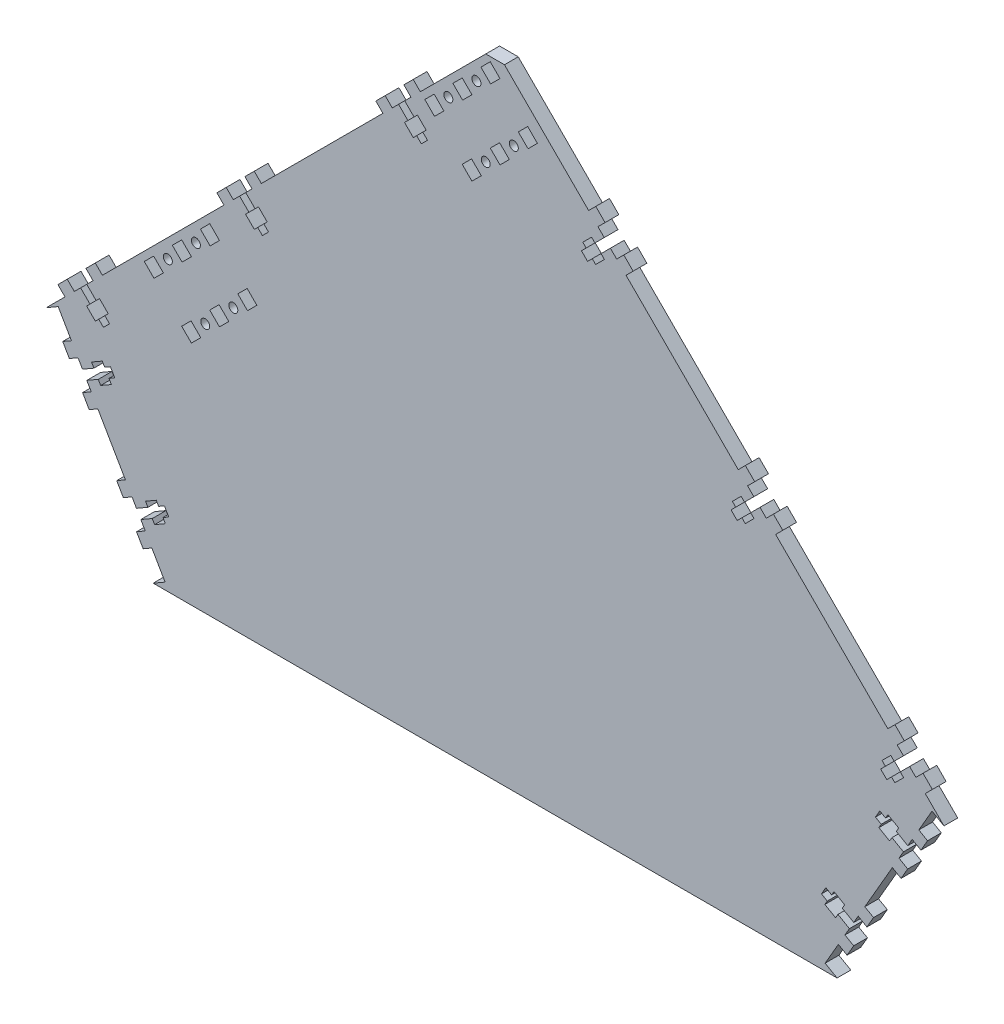
SolidWorks part; units mm, degrees
material "Acrylic (Blue)"
ref_plane "Front Plane" through (0, 0, 0) normal (0, 0, 1) x (1, 0, 0)
ref_plane "Top Plane" through (0, 0, 0) normal (0, 1, 0) x (1, 0, 0)
ref_plane "Right Plane" through (0, 0, 0) normal (1, 0, 0) x (0, 0, -1)
sketch "Sketch1" plane through (0, 0, 0) normal (0, 0, 1) x (1, 0, 0)
  line L0 (0, 0) -> (0, 304.4261) construction
  line L1 (0, 304.4261) -> (215.5261, 88.9)
  line L2 (215.5261, 88.9) -> (164.1997, 0)
  line L3 (164.1997, 0) -> (0, 0)
  line L4 (0, 304.4261) -> (-215.5261, 88.9)
  line L5 (-215.5261, 88.9) -> (-164.1997, 0)
  line L6 (-164.1997, 0) -> (0, 0)
  line L7 (-215.5261, 88.9) -> (215.5261, 88.9) construction
  line L8 (0, 304.4261) -> (3.5921, 308.0182) construction
  line L9 (3.5921, 308.0182) -> (219.1182, 92.4921) construction
  line L10 (219.1182, 92.4921) -> (215.5261, 88.9) construction
  line L11 (3.5921, 308.0182) -> (0, 311.6104) construction
  line L12 (0, 311.6104) -> (-219.1182, 92.4921) construction
  line L13 (-219.1182, 92.4921) -> (-215.5261, 88.9) construction
  line L14 (215.5261, 88.9) -> (219.9256, 86.36) construction
  line L15 (219.9256, 86.36) -> (168.5991, -2.54) construction
  line L16 (168.5991, -2.54) -> (164.1997, 0) construction
  line L17 (164.1997, 0) -> (164.1997, -12.7) construction
  line L18 (164.1997, -12.7) -> (-164.1997, -12.7) construction
  line L19 (-164.1997, -12.7) -> (-164.1997, 0) construction
  line L20 (-164.1997, 0) -> (-168.5991, -2.54) construction
  line L21 (-168.5991, -2.54) -> (-219.9256, 86.36) construction
  line L22 (-219.9256, 86.36) -> (-215.5261, 88.9) construction
  dimension "D1" = 304.8
  dimension "D2" = 120
  dimension "D3" = 88.9
  dimension "D4" = 5.08
  dimension "D5" = 12.7
extrude "Boss-Extrude1" add sketch "Sketch1" along normal blind 6.604
sketch "Sketch8" plane through (0, 0, 6.604) normal (0, 0, 1) x (1, 0, 0)
  line L0 (0, 304.4261) -> (-215.5261, 88.9) construction
  line L1 (215.5261, 88.9) -> (0, 304.4261) construction
  line B0 (-20.2954, 279.8202) -> (-15.8053, 284.3104)
  line B1 (-15.8053, 284.3104) -> (-11.1355, 279.6406)
  line B2 (-11.1355, 279.6406) -> (-15.6256, 275.1505)
  line B3 (-15.6256, 275.1505) -> (-20.2954, 279.8202)
  line B4 (-33.7658, 266.3499) -> (-29.2756, 270.84)
  line B5 (-29.2756, 270.84) -> (-24.6059, 266.1703)
  line B6 (-24.6059, 266.1703) -> (-29.096, 261.6801)
  line B7 (-29.096, 261.6801) -> (-33.7658, 266.3499)
  circle B8 centre (-22.4506, 272.9953) radius 2.1526
  line B9 (-13.4704, 281.9755) -> (-8.9803, 286.4656) construction
  circle B10 centre (-8.9803, 286.4656) radius 2.1527
  line B11 (-2.1553, 288.6209) -> (2.3349, 293.111)
  line B12 (-6.825, 293.2906) -> (-2.3349, 297.7808)
  line B13 (-2.3349, 297.7808) -> (2.3349, 293.111)
  line B14 (-6.825, 293.2906) -> (-2.1553, 288.6209)
  line B15 (-2.3349, 261.8597) -> (2.1553, 266.3499)
  line B16 (2.1553, 266.3499) -> (6.825, 261.6801)
  line B17 (6.825, 261.6801) -> (2.3349, 257.19)
  line B18 (2.3349, 257.19) -> (-2.3349, 261.8597)
  line B19 (-15.8053, 248.3893) -> (-11.3151, 252.8795)
  line B20 (-11.3151, 252.8795) -> (-6.6454, 248.2097)
  line B21 (-6.6454, 248.2097) -> (-11.1355, 243.7196)
  line B22 (-11.1355, 243.7196) -> (-15.8053, 248.3893)
  circle B23 centre (-4.4901, 255.0347) radius 2.1526
  circle B24 centre (8.9803, 268.5051) radius 2.1527
  line B25 (15.8053, 270.6604) -> (20.2954, 275.1505)
  line B26 (11.1355, 275.3301) -> (15.6256, 279.8202)
  line B27 (15.6256, 279.8202) -> (20.2954, 275.1505)
  line B28 (11.1355, 275.3301) -> (15.8053, 270.6604)
  line B29 (-154.9992, 145.1164) -> (-150.5091, 149.6065)
  line B30 (-150.5091, 149.6065) -> (-145.8394, 144.9368)
  line B31 (-145.8394, 144.9368) -> (-150.3295, 140.4467)
  line B32 (-150.3295, 140.4467) -> (-154.9992, 145.1164)
  line B33 (-168.4696, 131.646) -> (-163.9795, 136.1361)
  line B34 (-163.9795, 136.1361) -> (-159.3097, 131.4664)
  line B35 (-159.3097, 131.4664) -> (-163.7999, 126.9763)
  line B36 (-163.7999, 126.9763) -> (-168.4696, 131.646)
  circle B37 centre (-157.1545, 138.2914) radius 2.1526
  circle B38 centre (-143.6841, 151.7618) radius 2.1527
  line B39 (-136.8591, 153.9171) -> (-132.369, 158.4072)
  line B40 (-141.5288, 158.5868) -> (-137.0387, 163.0769)
  line B41 (-137.0387, 163.0769) -> (-132.369, 158.4072)
  line B42 (-141.5288, 158.5868) -> (-136.8591, 153.9171)
  line B43 (-137.0387, 127.1559) -> (-132.5486, 131.646)
  line B44 (-132.5486, 131.646) -> (-127.8788, 126.9763)
  line B45 (-127.8788, 126.9763) -> (-132.369, 122.4862)
  line B46 (-132.369, 122.4862) -> (-137.0387, 127.1559)
  line B47 (-150.5091, 113.6855) -> (-146.019, 118.1756)
  line B48 (-146.019, 118.1756) -> (-141.3492, 113.5059)
  line B49 (-141.3492, 113.5059) -> (-145.8394, 109.0158)
  line B50 (-145.8394, 109.0158) -> (-150.5091, 113.6855)
  circle B51 centre (-139.194, 120.3309) radius 2.1526
  circle B52 centre (-125.7236, 133.8013) radius 2.1527
  line B53 (-118.8986, 135.9565) -> (-114.4085, 140.4467)
  line B54 (-123.5683, 140.6263) -> (-119.0782, 145.1164)
  line B55 (-119.0782, 145.1164) -> (-114.4085, 140.4467)
  line B56 (-123.5683, 140.6263) -> (-118.8986, 135.9565)
  dimension "D1" = 25.4
  dimension "D2" = 6.35
  dimension "D3" = 6.35
  dimension "D4" = 190.5
sketch_block_instance "BOLT_HOLE_2X-1"
sketch_block "BOLT_HOLE_2X" parameters "D1"=4.3053, "D2"=6.35, "D3"=6.35, "D4"=6.604
sketch_block_instance "BOLT_HOLE_2X-2"
sketch_block_instance "BOLT_HOLE_2X-4"
sketch_block_instance "BOLT_HOLE_2X-5"
extrude "Cut-Extrude4" cut sketch "Sketch8" against normal through all
other "Move Face2" face at (107.7631, 196.6631, 3.302) parameters "D1"=0.0025
sketch "Sketch3" plane through (0, 0, 6.604) normal (0, 0, 1) x (1, 0, 0)
  line L0 (-209.8069, 92.202) -> (-215.5261, 88.9)
  line L1 (-215.5261, 88.9) -> (-164.1997, 0)
  line L2 (-164.1997, 0) -> (-158.4805, 3.302)
  line L3 (-158.4805, 3.302) -> (-209.8069, 92.202)
  line L4 (0, 304.4261) -> (0, 0) construction
  line L5 (158.4805, 3.302) -> (209.8069, 92.202)
  line L6 (164.1997, 0) -> (158.4805, 3.302)
  line L7 (215.5261, 88.9) -> (164.1997, 0)
  line L8 (209.8069, 92.202) -> (215.5261, 88.9)
  line L9 (0.0018, 304.4279) -> (-4.4883, 299.9378)
  line L10 (0.0018, 304.4279) -> (-215.5261, 88.9) construction
  line L11 (-4.4883, 299.9378) -> (4.4919, 299.9378)
  line L12 (215.5275, 88.9023) -> (0.0018, 304.4279) construction
  line L13 (4.4919, 299.9378) -> (0.0018, 304.4279)
  dimension "D1" = 6.604
  dimension "D2" = 6.35
extrude "Cut-Extrude2" cut sketch "Sketch3" against normal through all
sketch "Sketch4" plane through (0, 0, 6.604) normal (0, 0, 1) x (1, 0, 0)
  line L0 (-4.4883, 299.9378) -> (-215.5261, 88.9) construction
  line L1 (-57.294, 253.9571) -> (-115.6657, 195.5854) construction
  line L2 (-4.4883, 299.9378) -> (-215.5261, 88.9) construction
  line L3 (-133.6262, 177.6249) -> (-191.9979, 119.2533) construction
  line L6 (215.5275, 88.9023) -> (4.4919, 299.9378) construction
  line L7 (66.2756, 244.9791) -> (120.1571, 191.0976) construction
  line L8 (-158.4805, 3.302) -> (-209.8069, 92.202) construction
  line L9 (-209.8069, 92.202) -> (-215.5261, 88.9) construction
  line L10 (138.1177, 173.1371) -> (191.9992, 119.2555) construction
  line L11 (209.8069, 92.202) -> (158.4805, 3.302) construction
  line L12 (158.4805, 3.302) -> (164.1997, 0) construction
  line L13 (-164.1997, 0) -> (-158.4805, 3.302) construction
  line L14 (215.5261, 88.9) -> (209.8069, 92.202) construction
  line B0 (-46.374, 258.0521) -> (-41.8839, 253.562) construction
  line B1 (-41.8839, 253.562) -> (-43.5004, 251.9455) construction
  line B2 (-43.5004, 251.9455) -> (-39.2976, 247.7428) construction
  line B3 (-39.2976, 247.7428) -> (-37.6812, 249.3592) construction
  line B4 (-37.6812, 249.3592) -> (-35.4181, 247.0962) construction
  line B5 (-35.4181, 247.0962) -> (-32.4726, 250.0417) construction
  line B6 (-32.4726, 250.0417) -> (-34.7356, 252.3047) construction
  line B7 (-34.7356, 252.3047) -> (-33.1192, 253.9212) construction
  line B8 (-33.1192, 253.9212) -> (-37.3219, 258.1239) construction
  line B9 (-37.3219, 258.1239) -> (-38.9384, 256.5075) construction
  line B10 (-38.9384, 256.5075) -> (-43.4285, 260.9976) construction
  line B11 (-40.4112, 264.015) -> (-43.8236, 267.4275) construction
  line B12 (-43.8236, 267.4275) -> (-39.3335, 271.9176) construction
  line B13 (-39.3335, 271.9176) -> (-35.921, 268.5051) construction
  line B14 (-46.374, 258.0521) -> (-49.3914, 255.0347) construction
  line B15 (-49.3914, 255.0347) -> (-52.8039, 258.4472) construction
  line B16 (-52.8039, 258.4472) -> (-57.294, 253.9571) construction
  line B17 (-57.294, 253.9571) -> (-53.8815, 250.5446) construction
  line B18 (-43.4285, 260.9976) -> (-46.374, 258.0521) construction
  line B19 (-122.7062, 181.7199) -> (-118.2161, 177.2298) construction
  line B20 (-118.2161, 177.2298) -> (-119.8325, 175.6134) construction
  line B21 (-119.8325, 175.6134) -> (-115.6298, 171.4106) construction
  line B22 (-115.6298, 171.4106) -> (-114.0133, 173.027) construction
  line B23 (-114.0133, 173.027) -> (-111.7503, 170.764) construction
  line B24 (-111.7503, 170.764) -> (-108.8048, 173.7095) construction
  line B25 (-108.8048, 173.7095) -> (-111.0678, 175.9726) construction
  line B26 (-111.0678, 175.9726) -> (-109.4514, 177.589) construction
  line B27 (-109.4514, 177.589) -> (-113.6541, 181.7918) construction
  line B28 (-113.6541, 181.7918) -> (-115.2706, 180.1753) construction
  line B29 (-115.2706, 180.1753) -> (-119.7607, 184.6655) construction
  line B30 (-119.7607, 184.6655) -> (-116.7433, 187.6828) construction
  line B31 (-116.7433, 187.6828) -> (-120.1558, 191.0953) construction
  line B32 (-120.1558, 191.0953) -> (-115.6657, 195.5854) construction
  line B33 (-115.6657, 195.5854) -> (-112.2532, 192.1729) construction
  line B34 (-122.7062, 181.7199) -> (-125.7236, 178.7026) construction
  line B35 (-125.7236, 178.7026) -> (-129.1361, 182.1151) construction
  line B36 (-129.1361, 182.1151) -> (-133.6262, 177.6249) construction
  line B37 (-133.6262, 177.6249) -> (-130.2137, 174.2124) construction
  line B38 (-119.7607, 184.6655) -> (-122.7062, 181.7199) construction
  line B39 (-199.0384, 105.3878) -> (-194.5483, 100.8976) construction
  line B40 (-194.5483, 100.8976) -> (-196.1647, 99.2812) construction
  line B41 (-196.1647, 99.2812) -> (-191.962, 95.0784) construction
  line B42 (-191.962, 95.0784) -> (-190.3455, 96.6949) construction
  line B43 (-190.3455, 96.6949) -> (-188.0825, 94.4318) construction
  line B44 (-188.0825, 94.4318) -> (-185.137, 97.3774) construction
  line B45 (-185.137, 97.3774) -> (-187.4, 99.6404) construction
  line B46 (-187.4, 99.6404) -> (-185.7835, 101.2568) construction
  line B47 (-185.7835, 101.2568) -> (-189.9863, 105.4596) construction
  line B48 (-189.9863, 105.4596) -> (-191.6027, 103.8431) construction
  line B49 (-191.6027, 103.8431) -> (-196.0929, 108.3333) construction
  line B50 (-196.0929, 108.3333) -> (-193.0755, 111.3506) construction
  line B51 (-193.0755, 111.3506) -> (-196.488, 114.7631) construction
  line B52 (-196.488, 114.7631) -> (-191.9979, 119.2533) construction
  line B53 (-191.9979, 119.2533) -> (-188.5854, 115.8408) construction
  line B54 (-199.0384, 105.3878) -> (-202.0558, 102.3704) construction
  line B55 (-202.0558, 102.3704) -> (-205.4683, 105.7829) construction
  line B56 (-205.4683, 105.7829) -> (-209.9584, 101.2928) construction
  line B57 (-209.9584, 101.2928) -> (-206.5459, 97.8803) construction
  line B58 (-196.0929, 108.3333) -> (-199.0384, 105.3878) construction
  line B59 (-170.1391, 23.4953) -> (-164.6398, 26.6703) construction
  line B60 (-164.6398, 26.6703) -> (-163.4968, 24.6906) construction
  line B61 (-163.4968, 24.6906) -> (-158.3495, 27.6624) construction
  line B62 (-158.3495, 27.6624) -> (-159.4925, 29.6421) construction
  line B63 (-159.4925, 29.6421) -> (-156.7209, 31.2423) construction
  line B64 (-156.7209, 31.2423) -> (-158.8037, 34.8498) construction
  line B65 (-158.8037, 34.8498) -> (-161.5753, 33.2496) construction
  line B66 (-161.5753, 33.2496) -> (-162.7183, 35.2293) construction
  line B67 (-162.7183, 35.2293) -> (-167.8656, 32.2575) construction
  line B68 (-167.8656, 32.2575) -> (-166.7226, 30.2778) construction
  line B69 (-166.7226, 30.2778) -> (-172.2219, 27.1028) construction
  line B70 (-172.2219, 27.1028) -> (-174.3555, 30.7983) construction
  line B71 (-174.3555, 30.7983) -> (-178.5349, 28.3853) construction
  line B72 (-178.5349, 28.3853) -> (-181.7099, 33.8846) construction
  line B73 (-181.7099, 33.8846) -> (-177.5305, 36.2976) construction
  line B74 (-168.0055, 19.7998) -> (-172.1849, 17.3868) construction
  line B75 (-172.1849, 17.3868) -> (-169.0099, 11.8875) construction
  line B76 (-169.0099, 11.8875) -> (-164.8305, 14.3005) construction
  line B77 (-172.2219, 27.1028) -> (-170.1391, 23.4953) construction
  line B78 (-196.0655, 68.4012) -> (-190.5663, 71.5762) construction
  line B79 (-190.5663, 71.5762) -> (-189.4233, 69.5965) construction
  line B80 (-189.4233, 69.5965) -> (-184.2759, 72.5683) construction
  line B81 (-184.2759, 72.5683) -> (-185.4189, 74.548) construction
  line B82 (-185.4189, 74.548) -> (-182.6473, 76.1482) construction
  line B83 (-182.6473, 76.1482) -> (-184.7301, 79.7557) construction
  line B84 (-184.7301, 79.7557) -> (-187.5017, 78.1555) construction
  line B85 (-187.5017, 78.1555) -> (-188.6447, 80.1352) construction
  line B86 (-188.6447, 80.1352) -> (-193.7921, 77.1634) construction
  line B87 (-193.7921, 77.1634) -> (-192.6491, 75.1837) construction
  line B88 (-192.6491, 75.1837) -> (-198.1483, 72.0087) construction
  line B89 (-198.1483, 72.0087) -> (-200.2819, 75.7042) construction
  line B90 (-200.2819, 75.7042) -> (-204.4614, 73.2912) construction
  line B91 (-204.4614, 73.2912) -> (-207.6364, 78.7905) construction
  line B92 (-207.6364, 78.7905) -> (-203.4569, 81.2035) construction
  line B93 (-196.0655, 68.4012) -> (-193.9319, 64.7057) construction
  line B94 (-193.9319, 64.7057) -> (-198.1114, 62.2927) construction
  line B95 (-198.1114, 62.2927) -> (-194.9364, 56.7934) construction
  line B96 (-194.9364, 56.7934) -> (-190.7569, 59.2064) construction
  line B97 (-198.1483, 72.0087) -> (-196.0655, 68.4012) construction
  line B98 (172.2219, 27.1028) -> (166.7226, 30.2778) construction
  line B99 (166.7226, 30.2778) -> (167.8656, 32.2575) construction
  line B100 (167.8656, 32.2575) -> (162.7183, 35.2293) construction
  line B101 (162.7183, 35.2293) -> (161.5753, 33.2496) construction
  line B102 (161.5753, 33.2496) -> (158.8037, 34.8498) construction
  line B103 (158.8037, 34.8498) -> (156.7209, 31.2423) construction
  line B104 (156.7209, 31.2423) -> (159.4925, 29.6421) construction
  line B105 (159.4925, 29.6421) -> (158.3495, 27.6624) construction
  line B106 (158.3495, 27.6624) -> (163.4968, 24.6906) construction
  line B107 (163.4968, 24.6906) -> (164.6398, 26.6703) construction
  line B108 (164.6398, 26.6703) -> (170.1391, 23.4953) construction
  line B109 (168.0055, 19.7998) -> (172.1849, 17.3868) construction
  line B110 (172.1849, 17.3868) -> (169.0099, 11.8875) construction
  line B111 (169.0099, 11.8875) -> (164.8305, 14.3005) construction
  line B112 (172.2219, 27.1028) -> (174.3555, 30.7983) construction
  line B113 (174.3555, 30.7983) -> (178.5349, 28.3853) construction
  line B114 (178.5349, 28.3853) -> (181.7099, 33.8846) construction
  line B115 (181.7099, 33.8846) -> (177.5305, 36.2976) construction
  line B116 (170.1391, 23.4953) -> (172.2219, 27.1028) construction
  line B117 (198.1483, 72.0087) -> (192.6491, 75.1837) construction
  line B118 (192.6491, 75.1837) -> (193.7921, 77.1634) construction
  line B119 (193.7921, 77.1634) -> (188.6447, 80.1352) construction
  line B120 (188.6447, 80.1352) -> (187.5017, 78.1555) construction
  line B121 (187.5017, 78.1555) -> (184.7301, 79.7557) construction
  line B122 (184.7301, 79.7557) -> (182.6473, 76.1482) construction
  line B123 (182.6473, 76.1482) -> (185.4189, 74.548) construction
  line B124 (185.4189, 74.548) -> (184.2759, 72.5683) construction
  line B125 (184.2759, 72.5683) -> (189.4233, 69.5965) construction
  line B126 (189.4233, 69.5965) -> (190.5663, 71.5762) construction
  line B127 (190.5663, 71.5762) -> (196.0655, 68.4012) construction
  line B128 (196.0655, 68.4012) -> (193.9319, 64.7057) construction
  line B129 (193.9319, 64.7057) -> (198.1114, 62.2927) construction
  line B130 (198.1114, 62.2927) -> (194.9364, 56.7934) construction
  line B131 (194.9364, 56.7934) -> (190.7569, 59.2064) construction
  line B132 (200.2819, 75.7042) -> (204.4614, 73.2912) construction
  line B133 (204.4614, 73.2912) -> (207.6364, 78.7905) construction
  line B134 (207.6364, 78.7905) -> (203.4569, 81.2035) construction
  line B135 (196.0655, 68.4012) -> (198.1483, 72.0087) construction
  line B136 (196.0942, 108.3356) -> (191.6041, 103.8454) construction
  line B137 (191.6041, 103.8454) -> (189.9876, 105.4619) construction
  line B138 (189.9876, 105.4619) -> (185.7849, 101.2591) construction
  line B139 (185.7849, 101.2591) -> (187.4013, 99.6427) construction
  line B140 (187.4013, 99.6427) -> (185.1383, 97.3796) construction
  line B141 (185.1383, 97.3796) -> (188.0838, 94.4341) construction
  line B142 (188.0838, 94.4341) -> (190.3468, 96.6971) construction
  line B143 (190.3468, 96.6971) -> (191.9633, 95.0807) construction
  line B144 (191.9633, 95.0807) -> (196.166, 99.2835) construction
  line B145 (196.166, 99.2835) -> (194.5496, 100.8999) construction
  line B146 (194.5496, 100.8999) -> (199.0397, 105.39) construction
  line B147 (199.0397, 105.39) -> (202.0571, 102.3727) construction
  line B148 (202.0571, 102.3727) -> (205.4696, 105.7852) construction
  line B149 (205.4696, 105.7852) -> (209.9597, 101.295) construction
  line B150 (209.9597, 101.295) -> (206.5472, 97.8825) construction
  line B151 (196.0942, 108.3356) -> (193.0768, 111.3529) construction
  line B152 (193.0768, 111.3529) -> (196.4893, 114.7654) construction
  line B153 (196.4893, 114.7654) -> (191.9992, 119.2555) construction
  line B154 (191.9992, 119.2555) -> (188.5867, 115.843) construction
  line B155 (199.0397, 105.39) -> (196.0942, 108.3356) construction
  line B156 (124.2521, 180.1776) -> (119.762, 175.6875) construction
  line B157 (119.762, 175.6875) -> (118.1456, 177.3039) construction
  line B158 (118.1456, 177.3039) -> (113.9428, 173.1012) construction
  line B159 (113.9428, 173.1012) -> (115.5593, 171.4847) construction
  line B160 (115.5593, 171.4847) -> (113.2962, 169.2217) construction
  line B161 (113.2962, 169.2217) -> (116.2418, 166.2762) construction
  line B162 (116.2418, 166.2762) -> (118.5048, 168.5392) construction
  line B163 (118.5048, 168.5392) -> (120.1212, 166.9227) construction
  line B164 (120.1212, 166.9227) -> (124.324, 171.1255) construction
  line B165 (124.324, 171.1255) -> (122.7075, 172.7419) construction
  line B166 (122.7075, 172.7419) -> (127.1977, 177.2321) construction
  line B167 (127.1977, 177.2321) -> (130.215, 174.2147) construction
  line B168 (130.215, 174.2147) -> (133.6275, 177.6272) construction
  line B169 (133.6275, 177.6272) -> (138.1177, 173.1371) construction
  line B170 (138.1177, 173.1371) -> (134.7052, 169.7246) construction
  line B171 (124.2521, 180.1776) -> (121.2348, 183.195) construction
  line B172 (121.2348, 183.195) -> (124.6473, 186.6075) construction
  line B173 (124.6473, 186.6075) -> (120.1571, 191.0976) construction
  line B174 (120.1571, 191.0976) -> (116.7446, 187.6851) construction
  line B175 (127.1977, 177.2321) -> (124.2521, 180.1776) construction
  line B176 (52.4101, 252.0196) -> (47.92, 247.5295) construction
  line B177 (47.92, 247.5295) -> (46.3035, 249.146) construction
  line B178 (46.3035, 249.146) -> (42.1008, 244.9432) construction
  line B179 (42.1008, 244.9432) -> (43.7172, 243.3268) construction
  line B180 (43.7172, 243.3268) -> (41.4542, 241.0637) construction
  line B181 (41.4542, 241.0637) -> (44.3997, 238.1182) construction
  line B182 (44.3997, 238.1182) -> (46.6627, 240.3812) construction
  line B183 (46.6627, 240.3812) -> (48.2792, 238.7648) construction
  line B184 (48.2792, 238.7648) -> (52.4819, 242.9676) construction
  line B185 (52.4819, 242.9676) -> (50.8655, 244.584) construction
  line B186 (50.8655, 244.584) -> (55.3556, 249.0741) construction
  line B187 (55.3556, 249.0741) -> (58.373, 246.0568) construction
  line B188 (58.373, 246.0568) -> (61.7855, 249.4693) construction
  line B189 (61.7855, 249.4693) -> (66.2756, 244.9791) construction
  line B190 (66.2756, 244.9791) -> (62.8631, 241.5666) construction
  line B191 (52.4101, 252.0196) -> (49.3927, 255.037) construction
  line B192 (49.3927, 255.037) -> (52.8052, 258.4495) construction
  line B193 (52.8052, 258.4495) -> (48.3151, 262.9396) construction
  line B194 (48.3151, 262.9396) -> (44.9026, 259.5271) construction
  line B195 (55.3556, 249.0741) -> (52.4101, 252.0196) construction
  dimension "D1" = 12.7
  dimension "D2" = 241.3
  dimension "D3" = 228.6
  dimension "D4" = 12.7
  dimension "D5" = 12.7
  dimension "D6" = 12.7
  dimension "D7" = 12.7
  dimension "D8" = 12.7
sketch_block_instance "NUT_HOLE-1"
sketch_block "NUT_HOLE" parameters "D1"=6.35, "D2"=4.1656, "D3"=25.4, "D4"=4.826, "D5"=8.7376, "D6"=5.9436, "D7"=6.35, "D8"=20.32
sketch_block_instance "NUT_HOLE-2"
sketch_block_instance "NUT_HOLE-3"
sketch_block_instance "NUT_HOLE-9"
sketch_block_instance "NUT_HOLE-10"
sketch_block_instance "NUT_HOLE-11"
sketch_block_instance "NUT_HOLE-12"
sketch_block_instance "NUT_HOLE-13"
sketch_block_instance "NUT_HOLE-14"
sketch_block_instance "NUT_HOLE-15"
sketch "Sketch6" plane through (0, 0, 6.604) normal (0, 0, 1) x (1, 0, 0)
  line L110 (-38.9384, 256.5075) -> (-43.4285, 260.9976) construction
  line L111 (-37.3219, 258.1239) -> (-38.9384, 256.5075) construction
  line L112 (-33.1192, 253.9212) -> (-37.3219, 258.1239) construction
  line L113 (-34.7356, 252.3047) -> (-33.1192, 253.9212) construction
  line L114 (-32.4726, 250.0417) -> (-34.7356, 252.3047) construction
  line L115 (-35.4181, 247.0962) -> (-32.4726, 250.0417) construction
  line L116 (-37.6812, 249.3592) -> (-35.4181, 247.0962) construction
  line L117 (-39.2976, 247.7428) -> (-37.6812, 249.3592) construction
  line L118 (-43.5004, 251.9455) -> (-39.2976, 247.7428) construction
  line L119 (-41.8839, 253.562) -> (-43.5004, 251.9455) construction
  line L120 (-46.374, 258.0521) -> (-41.8839, 253.562) construction
  line L121 (-38.9384, 256.5075) -> (-43.4285, 260.9976)
  line L122 (-37.3219, 258.1239) -> (-38.9384, 256.5075)
  line L123 (-33.1192, 253.9212) -> (-37.3219, 258.1239)
  line L124 (-34.7356, 252.3047) -> (-33.1192, 253.9212)
  line L125 (-32.4726, 250.0417) -> (-34.7356, 252.3047)
  line L126 (-35.4181, 247.0962) -> (-32.4726, 250.0417)
  line L127 (-37.6812, 249.3592) -> (-35.4181, 247.0962)
  line L128 (-39.2976, 247.7428) -> (-37.6812, 249.3592)
  line L129 (-43.5004, 251.9455) -> (-39.2976, 247.7428)
  line L130 (-41.8839, 253.562) -> (-43.5004, 251.9455)
  line L131 (-46.374, 258.0521) -> (-41.8839, 253.562)
  line L132 (-115.2706, 180.1753) -> (-119.7607, 184.6655) construction
  line L133 (-122.7062, 181.7199) -> (-118.2161, 177.2298) construction
  line L134 (-118.2161, 177.2298) -> (-119.8325, 175.6134) construction
  line L135 (-119.8325, 175.6134) -> (-115.6298, 171.4106) construction
  line L136 (-115.6298, 171.4106) -> (-114.0133, 173.027) construction
  line L137 (-114.0133, 173.027) -> (-111.7503, 170.764) construction
  line L138 (-111.7503, 170.764) -> (-108.8048, 173.7095) construction
  line L139 (-108.8048, 173.7095) -> (-111.0678, 175.9726) construction
  line L140 (-111.0678, 175.9726) -> (-109.4514, 177.589) construction
  line L141 (-109.4514, 177.589) -> (-113.6541, 181.7918) construction
  line L142 (-113.6541, 181.7918) -> (-115.2706, 180.1753) construction
  line L143 (-115.2706, 180.1753) -> (-119.7607, 184.6655)
  line L144 (-122.7062, 181.7199) -> (-118.2161, 177.2298)
  line L145 (-118.2161, 177.2298) -> (-119.8325, 175.6134)
  line L146 (-119.8325, 175.6134) -> (-115.6298, 171.4106)
  line L147 (-115.6298, 171.4106) -> (-114.0133, 173.027)
  line L148 (-114.0133, 173.027) -> (-111.7503, 170.764)
  line L149 (-111.7503, 170.764) -> (-108.8048, 173.7095)
  line L150 (-108.8048, 173.7095) -> (-111.0678, 175.9726)
  line L151 (-111.0678, 175.9726) -> (-109.4514, 177.589)
  line L152 (-109.4514, 177.589) -> (-113.6541, 181.7918)
  line L153 (-113.6541, 181.7918) -> (-115.2706, 180.1753)
  line L154 (-191.6027, 103.8431) -> (-196.0929, 108.3333) construction
  line L155 (-199.0384, 105.3878) -> (-194.5483, 100.8976) construction
  line L156 (-194.5483, 100.8976) -> (-196.1647, 99.2812) construction
  line L157 (-196.1647, 99.2812) -> (-191.962, 95.0784) construction
  line L158 (-189.9863, 105.4596) -> (-191.6027, 103.8431) construction
  line L159 (-185.7835, 101.2568) -> (-189.9863, 105.4596) construction
  line L160 (-187.4, 99.6404) -> (-185.7835, 101.2568) construction
  line L161 (-185.137, 97.3774) -> (-187.4, 99.6404) construction
  line L162 (-188.0825, 94.4318) -> (-185.137, 97.3774) construction
  line L163 (-190.3455, 96.6949) -> (-188.0825, 94.4318) construction
  line L164 (-191.962, 95.0784) -> (-190.3455, 96.6949) construction
  line L165 (-192.6491, 75.1837) -> (-198.1483, 72.0087) construction
  line L166 (-193.7921, 77.1634) -> (-192.6491, 75.1837) construction
  line L167 (-188.6447, 80.1352) -> (-193.7921, 77.1634) construction
  line L168 (-184.7301, 79.7557) -> (-187.5017, 78.1555) construction
  line L169 (-182.6473, 76.1482) -> (-184.7301, 79.7557) construction
  line L170 (-187.5017, 78.1555) -> (-188.6447, 80.1352) construction
  line L171 (-185.4189, 74.548) -> (-182.6473, 76.1482) construction
  line L172 (-184.2759, 72.5683) -> (-185.4189, 74.548) construction
  line L173 (-189.4233, 69.5965) -> (-184.2759, 72.5683) construction
  line L174 (-190.5663, 71.5762) -> (-189.4233, 69.5965) construction
  line L175 (-196.0655, 68.4012) -> (-190.5663, 71.5762) construction
  line L176 (-191.6027, 103.8431) -> (-196.0929, 108.3333)
  line L177 (-199.0384, 105.3878) -> (-194.5483, 100.8976)
  line L178 (-194.5483, 100.8976) -> (-196.1647, 99.2812)
  line L179 (-196.1647, 99.2812) -> (-191.962, 95.0784)
  line L180 (-189.9863, 105.4596) -> (-191.6027, 103.8431)
  line L181 (-185.7835, 101.2568) -> (-189.9863, 105.4596)
  line L182 (-187.4, 99.6404) -> (-185.7835, 101.2568)
  line L183 (-185.137, 97.3774) -> (-187.4, 99.6404)
  line L184 (-188.0825, 94.4318) -> (-185.137, 97.3774)
  line L185 (-190.3455, 96.6949) -> (-188.0825, 94.4318)
  line L186 (-191.962, 95.0784) -> (-190.3455, 96.6949)
  line L187 (-192.6491, 75.1837) -> (-198.1483, 72.0087)
  line L188 (-193.7921, 77.1634) -> (-192.6491, 75.1837)
  line L189 (-188.6447, 80.1352) -> (-193.7921, 77.1634)
  line L190 (-184.7301, 79.7557) -> (-187.5017, 78.1555)
  line L191 (-182.6473, 76.1482) -> (-184.7301, 79.7557)
  line L192 (-187.5017, 78.1555) -> (-188.6447, 80.1352)
  line L193 (-185.4189, 74.548) -> (-182.6473, 76.1482)
  line L194 (-184.2759, 72.5683) -> (-185.4189, 74.548)
  line L195 (-189.4233, 69.5965) -> (-184.2759, 72.5683)
  line L196 (-190.5663, 71.5762) -> (-189.4233, 69.5965)
  line L197 (-196.0655, 68.4012) -> (-190.5663, 71.5762)
  line L198 (-166.7226, 30.2778) -> (-172.2219, 27.1028) construction
  line L199 (-167.8656, 32.2575) -> (-166.7226, 30.2778) construction
  line L200 (-162.7183, 35.2293) -> (-167.8656, 32.2575) construction
  line L201 (-161.5753, 33.2496) -> (-162.7183, 35.2293) construction
  line L202 (-158.8037, 34.8498) -> (-161.5753, 33.2496) construction
  line L203 (-156.7209, 31.2423) -> (-158.8037, 34.8498) construction
  line L204 (-159.4925, 29.6421) -> (-156.7209, 31.2423) construction
  line L205 (-158.3495, 27.6624) -> (-159.4925, 29.6421) construction
  line L206 (-163.4968, 24.6906) -> (-158.3495, 27.6624) construction
  line L207 (-164.6398, 26.6703) -> (-163.4968, 24.6906) construction
  line L208 (-170.1391, 23.4953) -> (-164.6398, 26.6703) construction
  line L209 (-166.7226, 30.2778) -> (-172.2219, 27.1028)
  line L210 (-167.8656, 32.2575) -> (-166.7226, 30.2778)
  line L211 (-162.7183, 35.2293) -> (-167.8656, 32.2575)
  line L212 (-161.5753, 33.2496) -> (-162.7183, 35.2293)
  line L213 (-158.8037, 34.8498) -> (-161.5753, 33.2496)
  line L214 (-156.7209, 31.2423) -> (-158.8037, 34.8498)
  line L215 (-159.4925, 29.6421) -> (-156.7209, 31.2423)
  line L216 (-158.3495, 27.6624) -> (-159.4925, 29.6421)
  line L217 (-163.4968, 24.6906) -> (-158.3495, 27.6624)
  line L218 (-164.6398, 26.6703) -> (-163.4968, 24.6906)
  line L219 (-170.1391, 23.4953) -> (-164.6398, 26.6703)
  line L220 (158.3495, 27.6624) -> (163.4968, 24.6906) construction
  line L221 (159.4925, 29.6421) -> (158.3495, 27.6624) construction
  line L222 (156.7209, 31.2423) -> (159.4925, 29.6421) construction
  line L223 (158.8037, 34.8498) -> (156.7209, 31.2423) construction
  line L224 (161.5753, 33.2496) -> (158.8037, 34.8498) construction
  line L225 (167.8656, 32.2575) -> (162.7183, 35.2293) construction
  line L226 (162.7183, 35.2293) -> (161.5753, 33.2496) construction
  line L227 (172.2219, 27.1028) -> (166.7226, 30.2778) construction
  line L228 (164.6398, 26.6703) -> (170.1391, 23.4953) construction
  line L229 (163.4968, 24.6906) -> (164.6398, 26.6703) construction
  line L230 (166.7226, 30.2778) -> (167.8656, 32.2575) construction
  line L231 (198.1483, 72.0087) -> (192.6491, 75.1837) construction
  line L232 (192.6491, 75.1837) -> (193.7921, 77.1634) construction
  line L233 (193.7921, 77.1634) -> (188.6447, 80.1352) construction
  line L234 (188.6447, 80.1352) -> (187.5017, 78.1555) construction
  line L235 (187.5017, 78.1555) -> (184.7301, 79.7557) construction
  line L236 (184.7301, 79.7557) -> (182.6473, 76.1482) construction
  line L237 (182.6473, 76.1482) -> (185.4189, 74.548) construction
  line L238 (185.4189, 74.548) -> (184.2759, 72.5683) construction
  line L239 (184.2759, 72.5683) -> (189.4233, 69.5965) construction
  line L240 (189.4233, 69.5965) -> (190.5663, 71.5762) construction
  line L241 (190.5663, 71.5762) -> (196.0655, 68.4012) construction
  line L242 (158.3495, 27.6624) -> (163.4968, 24.6906)
  line L243 (159.4925, 29.6421) -> (158.3495, 27.6624)
  line L244 (156.7209, 31.2423) -> (159.4925, 29.6421)
  line L245 (158.8037, 34.8498) -> (156.7209, 31.2423)
  line L246 (161.5753, 33.2496) -> (158.8037, 34.8498)
  line L247 (167.8656, 32.2575) -> (162.7183, 35.2293)
  line L248 (162.7183, 35.2293) -> (161.5753, 33.2496)
  line L249 (172.2219, 27.1028) -> (166.7226, 30.2778)
  line L250 (164.6398, 26.6703) -> (170.1391, 23.4953)
  line L251 (163.4968, 24.6906) -> (164.6398, 26.6703)
  line L252 (166.7226, 30.2778) -> (167.8656, 32.2575)
  line L253 (198.1483, 72.0087) -> (192.6491, 75.1837)
  line L254 (192.6491, 75.1837) -> (193.7921, 77.1634)
  line L255 (193.7921, 77.1634) -> (188.6447, 80.1352)
  line L256 (188.6447, 80.1352) -> (187.5017, 78.1555)
  line L257 (187.5017, 78.1555) -> (184.7301, 79.7557)
  line L258 (184.7301, 79.7557) -> (182.6473, 76.1482)
  line L259 (182.6473, 76.1482) -> (185.4189, 74.548)
  line L260 (185.4189, 74.548) -> (184.2759, 72.5683)
  line L261 (184.2759, 72.5683) -> (189.4233, 69.5965)
  line L262 (189.4233, 69.5965) -> (190.5663, 71.5762)
  line L263 (190.5663, 71.5762) -> (196.0655, 68.4012)
  line L264 (187.4013, 99.6427) -> (185.1383, 97.3796) construction
  line L265 (185.1383, 97.3796) -> (188.0838, 94.4341) construction
  line L266 (188.0838, 94.4341) -> (190.3468, 96.6971) construction
  line L267 (190.3468, 96.6971) -> (191.9633, 95.0807) construction
  line L268 (191.9633, 95.0807) -> (196.166, 99.2835) construction
  line L269 (196.166, 99.2835) -> (194.5496, 100.8999) construction
  line L270 (194.5496, 100.8999) -> (199.0397, 105.39) construction
  line L271 (196.0942, 108.3356) -> (191.6041, 103.8454) construction
  line L272 (191.6041, 103.8454) -> (189.9876, 105.4619) construction
  line L273 (189.9876, 105.4619) -> (185.7849, 101.2591) construction
  line L274 (185.7849, 101.2591) -> (187.4013, 99.6427) construction
  line L275 (187.4013, 99.6427) -> (185.1383, 97.3796)
  line L276 (185.1383, 97.3796) -> (188.0838, 94.4341)
  line L277 (188.0838, 94.4341) -> (190.3468, 96.6971)
  line L278 (190.3468, 96.6971) -> (191.9633, 95.0807)
  line L279 (191.9633, 95.0807) -> (196.166, 99.2835)
  line L280 (196.166, 99.2835) -> (194.5496, 100.8999)
  line L281 (194.5496, 100.8999) -> (199.0397, 105.39)
  line L282 (196.0942, 108.3356) -> (191.6041, 103.8454)
  line L283 (191.6041, 103.8454) -> (189.9876, 105.4619)
  line L284 (189.9876, 105.4619) -> (185.7849, 101.2591)
  line L285 (185.7849, 101.2591) -> (187.4013, 99.6427)
  line L286 (124.2521, 180.1776) -> (119.762, 175.6875) construction
  line L287 (119.762, 175.6875) -> (118.1456, 177.3039) construction
  line L288 (118.1456, 177.3039) -> (113.9428, 173.1012) construction
  line L289 (113.9428, 173.1012) -> (115.5593, 171.4847) construction
  line L290 (115.5593, 171.4847) -> (113.2962, 169.2217) construction
  line L291 (113.2962, 169.2217) -> (116.2418, 166.2762) construction
  line L292 (116.2418, 166.2762) -> (118.5048, 168.5392) construction
  line L293 (118.5048, 168.5392) -> (120.1212, 166.9227) construction
  line L294 (120.1212, 166.9227) -> (124.324, 171.1255) construction
  line L295 (124.324, 171.1255) -> (122.7075, 172.7419) construction
  line L296 (122.7075, 172.7419) -> (127.1977, 177.2321) construction
  line L297 (124.2521, 180.1776) -> (119.762, 175.6875)
  line L298 (119.762, 175.6875) -> (118.1456, 177.3039)
  line L299 (118.1456, 177.3039) -> (113.9428, 173.1012)
  line L300 (113.9428, 173.1012) -> (115.5593, 171.4847)
  line L301 (115.5593, 171.4847) -> (113.2962, 169.2217)
  line L302 (113.2962, 169.2217) -> (116.2418, 166.2762)
  line L303 (116.2418, 166.2762) -> (118.5048, 168.5392)
  line L304 (118.5048, 168.5392) -> (120.1212, 166.9227)
  line L305 (120.1212, 166.9227) -> (124.324, 171.1255)
  line L306 (124.324, 171.1255) -> (122.7075, 172.7419)
  line L307 (122.7075, 172.7419) -> (127.1977, 177.2321)
  line L308 (41.4542, 241.0637) -> (44.3997, 238.1182) construction
  line L309 (44.3997, 238.1182) -> (46.6627, 240.3812) construction
  line L310 (46.6627, 240.3812) -> (48.2792, 238.7648) construction
  line L311 (48.2792, 238.7648) -> (52.4819, 242.9676) construction
  line L312 (50.8655, 244.584) -> (55.3556, 249.0741) construction
  line L313 (52.4819, 242.9676) -> (50.8655, 244.584) construction
  line L314 (52.4101, 252.0196) -> (47.92, 247.5295) construction
  line L315 (47.92, 247.5295) -> (46.3035, 249.146) construction
  line L316 (46.3035, 249.146) -> (42.1008, 244.9432) construction
  line L317 (42.1008, 244.9432) -> (43.7172, 243.3268) construction
  line L318 (43.7172, 243.3268) -> (41.4542, 241.0637) construction
  line L319 (41.4542, 241.0637) -> (44.3997, 238.1182)
  line L320 (44.3997, 238.1182) -> (46.6627, 240.3812)
  line L321 (46.6627, 240.3812) -> (48.2792, 238.7648)
  line L322 (48.2792, 238.7648) -> (52.4819, 242.9676)
  line L323 (50.8655, 244.584) -> (55.3556, 249.0741)
  line L324 (52.4819, 242.9676) -> (50.8655, 244.584)
  line L325 (52.4101, 252.0196) -> (47.92, 247.5295)
  line L326 (47.92, 247.5295) -> (46.3035, 249.146)
  line L327 (46.3035, 249.146) -> (42.1008, 244.9432)
  line L328 (42.1008, 244.9432) -> (43.7172, 243.3268)
  line L329 (43.7172, 243.3268) -> (41.4542, 241.0637)
  line L330 (-43.4285, 260.9976) -> (-46.374, 258.0521)
  line L331 (-119.7607, 184.6655) -> (-122.7062, 181.7199)
  line L332 (-196.0929, 108.3333) -> (-199.0384, 105.3878)
  line L333 (-198.1483, 72.0087) -> (-196.0655, 68.4012)
  line L334 (-172.2219, 27.1028) -> (-170.1391, 23.4953)
  line L335 (170.1391, 23.4953) -> (172.2219, 27.1028)
  line L336 (196.0655, 68.4012) -> (198.1483, 72.0087)
  line L337 (196.0942, 108.3356) -> (199.0397, 105.39)
  line L338 (124.2521, 180.1776) -> (127.1977, 177.2321)
  line L339 (52.4101, 252.0196) -> (55.3556, 249.0741)
  point P61 (162.7183, 35.2293)
extrude "Cut-Extrude3" cut sketch "Sketch6" against normal through all
sketch "Sketch7" plane through (0, 0, 6.604) normal (0, 0, 1) x (1, 0, 0)
  line L60 (-39.3335, 271.9176) -> (-35.921, 268.5051) construction
  line L61 (-43.8236, 267.4275) -> (-39.3335, 271.9176) construction
  line L62 (-40.4112, 264.015) -> (-43.8236, 267.4275) construction
  line L63 (-49.3914, 255.0347) -> (-52.8039, 258.4472) construction
  line L64 (-52.8039, 258.4472) -> (-57.294, 253.9571) construction
  line L65 (-57.294, 253.9571) -> (-53.8815, 250.5446) construction
  line L66 (-115.6657, 195.5854) -> (-112.2532, 192.1729) construction
  line L67 (-120.1558, 191.0953) -> (-115.6657, 195.5854) construction
  line L68 (-116.7433, 187.6828) -> (-120.1558, 191.0953) construction
  line L69 (-125.7236, 178.7026) -> (-129.1361, 182.1151) construction
  line L70 (-129.1361, 182.1151) -> (-133.6262, 177.6249) construction
  line L71 (-133.6262, 177.6249) -> (-130.2137, 174.2124) construction
  line L72 (-191.9979, 119.2533) -> (-188.5854, 115.8408) construction
  line L73 (-196.488, 114.7631) -> (-191.9979, 119.2533) construction
  line L74 (-193.0755, 111.3506) -> (-196.488, 114.7631) construction
  line L75 (-202.0558, 102.3704) -> (-205.4683, 105.7829) construction
  line L76 (-205.4683, 105.7829) -> (-209.9584, 101.2928) construction
  line L77 (-209.9584, 101.2928) -> (-206.5459, 97.8803) construction
  line L78 (-207.6364, 78.7905) -> (-203.4569, 81.2035) construction
  line L79 (-204.4614, 73.2912) -> (-207.6364, 78.7905) construction
  line L80 (-200.2819, 75.7042) -> (-204.4614, 73.2912) construction
  line L81 (-39.3335, 271.9176) -> (-35.921, 268.5051)
  line L82 (-43.8236, 267.4275) -> (-39.3335, 271.9176)
  line L83 (-40.4112, 264.015) -> (-43.8236, 267.4275)
  line L84 (-49.3914, 255.0347) -> (-52.8039, 258.4472)
  line L85 (-52.8039, 258.4472) -> (-57.294, 253.9571)
  line L86 (-57.294, 253.9571) -> (-53.8815, 250.5446)
  line L87 (-115.6657, 195.5854) -> (-112.2532, 192.1729)
  line L88 (-120.1558, 191.0953) -> (-115.6657, 195.5854)
  line L89 (-116.7433, 187.6828) -> (-120.1558, 191.0953)
  line L90 (-125.7236, 178.7026) -> (-129.1361, 182.1151)
  line L91 (-129.1361, 182.1151) -> (-133.6262, 177.6249)
  line L92 (-133.6262, 177.6249) -> (-130.2137, 174.2124)
  line L93 (-191.9979, 119.2533) -> (-188.5854, 115.8408)
  line L94 (-196.488, 114.7631) -> (-191.9979, 119.2533)
  line L95 (-193.0755, 111.3506) -> (-196.488, 114.7631)
  line L96 (-202.0558, 102.3704) -> (-205.4683, 105.7829)
  line L97 (-205.4683, 105.7829) -> (-209.9584, 101.2928)
  line L98 (-209.9584, 101.2928) -> (-206.5459, 97.8803)
  line L99 (-207.6364, 78.7905) -> (-203.4569, 81.2035)
  line L100 (-204.4614, 73.2912) -> (-207.6364, 78.7905)
  line L101 (-200.2819, 75.7042) -> (-204.4614, 73.2912)
  line L102 (-193.9319, 64.7057) -> (-198.1114, 62.2927) construction
  line L103 (-198.1114, 62.2927) -> (-194.9364, 56.7934) construction
  line L104 (-194.9364, 56.7934) -> (-190.7569, 59.2064) construction
  line L105 (-178.5349, 28.3853) -> (-181.7099, 33.8846) construction
  line L106 (-181.7099, 33.8846) -> (-177.5305, 36.2976) construction
  line L107 (-174.3555, 30.7983) -> (-178.5349, 28.3853) construction
  line L108 (-172.1849, 17.3868) -> (-169.0099, 11.8875) construction
  line L109 (-168.0055, 19.7998) -> (-172.1849, 17.3868) construction
  line L110 (-169.0099, 11.8875) -> (-164.8305, 14.3005) construction
  line L111 (169.0099, 11.8875) -> (164.8305, 14.3005) construction
  line L112 (172.1849, 17.3868) -> (169.0099, 11.8875) construction
  line L113 (168.0055, 19.7998) -> (172.1849, 17.3868) construction
  line L114 (181.7099, 33.8846) -> (177.5305, 36.2976) construction
  line L115 (178.5349, 28.3853) -> (181.7099, 33.8846) construction
  line L116 (174.3555, 30.7983) -> (178.5349, 28.3853) construction
  line L117 (193.9319, 64.7057) -> (198.1114, 62.2927) construction
  line L118 (198.1114, 62.2927) -> (194.9364, 56.7934) construction
  line L119 (194.9364, 56.7934) -> (190.7569, 59.2064) construction
  line L120 (207.6364, 78.7905) -> (203.4569, 81.2035) construction
  line L121 (200.2819, 75.7042) -> (204.4614, 73.2912) construction
  line L122 (204.4614, 73.2912) -> (207.6364, 78.7905) construction
  line L123 (-193.9319, 64.7057) -> (-198.1114, 62.2927)
  line L124 (-198.1114, 62.2927) -> (-194.9364, 56.7934)
  line L125 (-194.9364, 56.7934) -> (-190.7569, 59.2064)
  line L126 (-178.5349, 28.3853) -> (-181.7099, 33.8846)
  line L127 (-181.7099, 33.8846) -> (-177.5305, 36.2976)
  line L128 (-174.3555, 30.7983) -> (-178.5349, 28.3853)
  line L129 (-172.1849, 17.3868) -> (-169.0099, 11.8875)
  line L130 (-168.0055, 19.7998) -> (-172.1849, 17.3868)
  line L131 (-169.0099, 11.8875) -> (-164.8305, 14.3005)
  line L132 (169.0099, 11.8875) -> (164.8305, 14.3005)
  line L133 (172.1849, 17.3868) -> (169.0099, 11.8875)
  line L134 (168.0055, 19.7998) -> (172.1849, 17.3868)
  line L135 (181.7099, 33.8846) -> (177.5305, 36.2976)
  line L136 (178.5349, 28.3853) -> (181.7099, 33.8846)
  line L137 (174.3555, 30.7983) -> (178.5349, 28.3853)
  line L138 (193.9319, 64.7057) -> (198.1114, 62.2927)
  line L139 (198.1114, 62.2927) -> (194.9364, 56.7934)
  line L140 (194.9364, 56.7934) -> (190.7569, 59.2064)
  line L141 (207.6364, 78.7905) -> (203.4569, 81.2035)
  line L142 (200.2819, 75.7042) -> (204.4614, 73.2912)
  line L143 (204.4614, 73.2912) -> (207.6364, 78.7905)
  line L144 (209.9597, 101.295) -> (206.5472, 97.8825) construction
  line L145 (205.4696, 105.7852) -> (209.9597, 101.295) construction
  line L146 (202.0571, 102.3727) -> (205.4696, 105.7852) construction
  line L147 (193.0768, 111.3529) -> (196.4893, 114.7654) construction
  line L148 (196.4893, 114.7654) -> (191.9992, 119.2555) construction
  line L149 (191.9992, 119.2555) -> (188.5867, 115.843) construction
  line L150 (130.215, 174.2147) -> (133.6275, 177.6272) construction
  line L151 (133.6275, 177.6272) -> (138.1177, 173.1371) construction
  line L152 (138.1177, 173.1371) -> (134.7052, 169.7246) construction
  line L153 (121.2348, 183.195) -> (124.6473, 186.6075) construction
  line L154 (124.6473, 186.6075) -> (120.1571, 191.0976) construction
  line L155 (120.1571, 191.0976) -> (116.7446, 187.6851) construction
  line L156 (209.9597, 101.295) -> (206.5472, 97.8825)
  line L157 (205.4696, 105.7852) -> (209.9597, 101.295)
  line L158 (202.0571, 102.3727) -> (205.4696, 105.7852)
  line L159 (193.0768, 111.3529) -> (196.4893, 114.7654)
  line L160 (196.4893, 114.7654) -> (191.9992, 119.2555)
  line L161 (191.9992, 119.2555) -> (188.5867, 115.843)
  line L162 (130.215, 174.2147) -> (133.6275, 177.6272)
  line L163 (133.6275, 177.6272) -> (138.1177, 173.1371)
  line L164 (138.1177, 173.1371) -> (134.7052, 169.7246)
  line L165 (121.2348, 183.195) -> (124.6473, 186.6075)
  line L166 (124.6473, 186.6075) -> (120.1571, 191.0976)
  line L167 (120.1571, 191.0976) -> (116.7446, 187.6851)
  line L168 (48.3151, 262.9396) -> (44.9026, 259.5271) construction
  line L169 (52.8052, 258.4495) -> (48.3151, 262.9396) construction
  line L170 (49.3927, 255.037) -> (52.8052, 258.4495) construction
  line L171 (58.373, 246.0568) -> (61.7855, 249.4693) construction
  line L172 (61.7855, 249.4693) -> (66.2756, 244.9791) construction
  line L173 (66.2756, 244.9791) -> (62.8631, 241.5666) construction
  line L174 (48.3151, 262.9396) -> (44.9026, 259.5271)
  line L175 (52.8052, 258.4495) -> (48.3151, 262.9396)
  line L176 (49.3927, 255.037) -> (52.8052, 258.4495)
  line L177 (58.373, 246.0568) -> (61.7855, 249.4693)
  line L178 (61.7855, 249.4693) -> (66.2756, 244.9791)
  line L179 (66.2756, 244.9791) -> (62.8631, 241.5666)
  line L180 (44.9026, 259.5271) -> (49.3927, 255.037)
  line L181 (58.373, 246.0568) -> (62.8631, 241.5666)
  line L182 (116.7446, 187.6851) -> (121.2348, 183.195)
  line L183 (130.215, 174.2147) -> (134.7052, 169.7246)
  line L184 (188.5867, 115.843) -> (193.0768, 111.3529)
  line L185 (202.0571, 102.3727) -> (206.5472, 97.8825)
  line L186 (203.4569, 81.2035) -> (200.2819, 75.7042)
  line L187 (193.9319, 64.7057) -> (190.7569, 59.2064)
  line L188 (177.5305, 36.2976) -> (174.3555, 30.7983)
  line L189 (-168.0055, 19.7998) -> (-164.8305, 14.3005)
  line L190 (168.0055, 19.7998) -> (164.8305, 14.3005)
  line L191 (-177.5305, 36.2976) -> (-174.3555, 30.7983)
  line L192 (-193.9319, 64.7057) -> (-190.7569, 59.2064)
  line L193 (-203.4569, 81.2035) -> (-200.2819, 75.7042)
  line L194 (-206.5459, 97.8803) -> (-202.0558, 102.3704)
  line L195 (-193.0755, 111.3506) -> (-188.5854, 115.8408)
  line L196 (-130.2137, 174.2124) -> (-125.7236, 178.7026)
  line L197 (-116.7433, 187.6828) -> (-112.2532, 192.1729)
  line L198 (-35.921, 268.5051) -> (-40.4112, 264.015)
  line L199 (-49.3914, 255.0347) -> (-53.8815, 250.5446)
extrude "Boss-Extrude2" add sketch "Sketch7" against normal up to surface (6.604 mm away) up to face at (2.8796, 123.2157, 0)
hole_wizard "CSK for #8 Flat Head Socket Cap Screw1" positions "Sketch11" profile "Sketch10" countersink size "#8" standard "ANSI Inch" end condition through all
sketch "Sketch11" plane through (0, 0, 0) normal (0, 0, -1) x (-1, 0, 0)
  point P0 (8.9803, 286.4656)
  point P3 (22.4506, 272.9953)
  point P6 (4.4901, 255.0347)
  point P9 (-8.9803, 268.5051)
  point P12 (143.6841, 151.7618)
  point P15 (157.1545, 138.2914)
  point P18 (125.7236, 133.8013)
  point P21 (139.194, 120.3309)
sketch "Sketch10" plane through (-8.9803, 286.4656, 0) normal (1, 0, 0) x (0, 1, 0)
  line L0 (0, 0) -> (0, 6.604)
  line L1 (0, 6.604) -> (2.1526, 6.604)
  line L2 (2.1526, 6.604) -> (2.1526, 2.7685)
  line L3 (2.1526, 2.7685) -> (4.5593, 0)
  line L5 (4.5593, 0) -> (0, 0)
  line L6 (-2.1526, 2.7685) -> (-4.5593, 0) construction
  line L11 (0, -6.35) -> (0, 107.95) construction
  dimension "Thru Hole Dia." = 4.3053
  dimension "Thru Hole Depth" = 6.604
  dimension "Near C'Sink Dia." = 9.1186
  dimension "Near C'Sink Angle" = 82
other "Move Face3" [suppressed] parameters "D1"=0.0508
